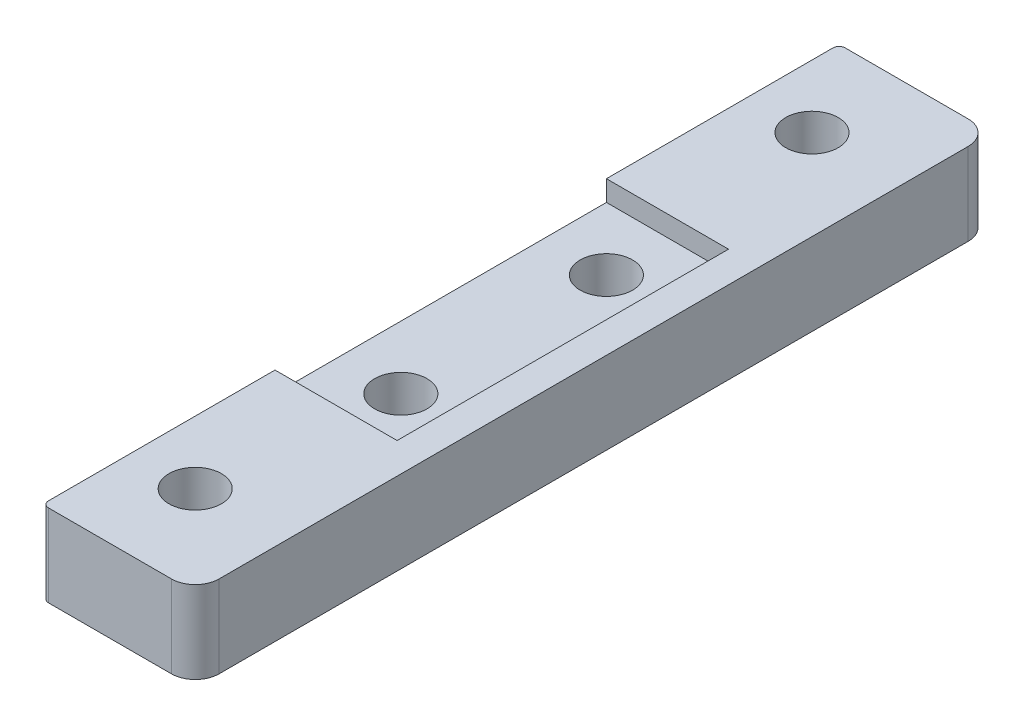
SolidWorks part; units mm, degrees
ref_plane "Front" through (0, 0, 0) normal (0, 0, 1) x (1, 0, 0)
ref_plane "Top" through (0, 0, 0) normal (0, 1, 0) x (1, 0, 0)
ref_plane "Right" through (0, 0, 0) normal (1, 0, 0) x (0, 0, -1)
sketch "Sketch1" plane through (0, 0, 0) normal (0, 1, 0) x (1, 0, 0)
  line L0 (-6.5823, 38.7525) -> (8.2948, 38.7525) construction
  line L1 (-5.9773, 0) -> (5.9773, 0)
  line L2 (-6.5823, 0.605) -> (-6.5823, 76.9)
  line L3 (-5.9773, 77.505) -> (5.9773, 77.505)
  line L4 (8.2948, 2.3175) -> (8.2948, 75.1875)
  line L5 (-0.4652, 77.505) -> (-0.4652, 0) construction
  arc A0 (-5.9773, 77.505) -> (-6.5823, 76.9) centre (-5.9772, 76.9) ccw
  arc A1 (8.2948, 75.1875) -> (5.9773, 77.505) centre (5.9773, 75.1875) ccw
  arc A2 (5.9773, 0) -> (8.2948, 2.3175) centre (5.9773, 2.3175) ccw
  arc A3 (-6.5823, 0.605) -> (-5.9773, 0) centre (-5.9772, 0.605) ccw
  circle A4 centre (-0.4653, 68.7525) radius 2.55
  circle A5 centre (-0.4652, 48.7525) radius 2.55
  circle A6 centre (-0.4653, 8.7525) radius 2.55
  circle A7 centre (-0.4652, 28.7525) radius 2.55
  dimension "D1" = 1.21
  dimension "D2" = 4.635
  dimension "D5" = 5.1
  dimension "D6" = 5.1
  dimension "D3" = 77.505
  dimension "D4" = 14.877
  dimension "D7" = 20
  dimension "D8" = 20
  dimension "D9" = 8.76
extrude "Boss-Extrude1" add sketch "Sketch1" along normal blind 8
sketch "Sketch2" plane through (0, 8, 0) normal (0, 1, 0) x (1, 0, 0)
  line L0 (-6.5823, 38.7525) -> (8.2948, 38.7525) construction
  line L1 (-6.5823, 76.9) -> (-6.5823, 0.605) construction
  line L2 (8.2948, 2.3175) -> (8.2948, 75.1875) construction
  line L4 (-6.5823, 54.8725) -> (5.2947, 54.8725)
  line L5 (-6.5823, 54.8725) -> (-6.5823, 22.6325)
  line L6 (-6.5823, 22.6325) -> (5.2947, 22.6325)
  line L7 (5.2947, 54.8725) -> (5.2947, 22.6325)
  point P10 (5.2947, 38.7525)
  dimension "D1" = 32.24
  dimension "D2" = 11.877
extrude "Cut-Extrude1" cut sketch "Sketch2" against normal blind 2
